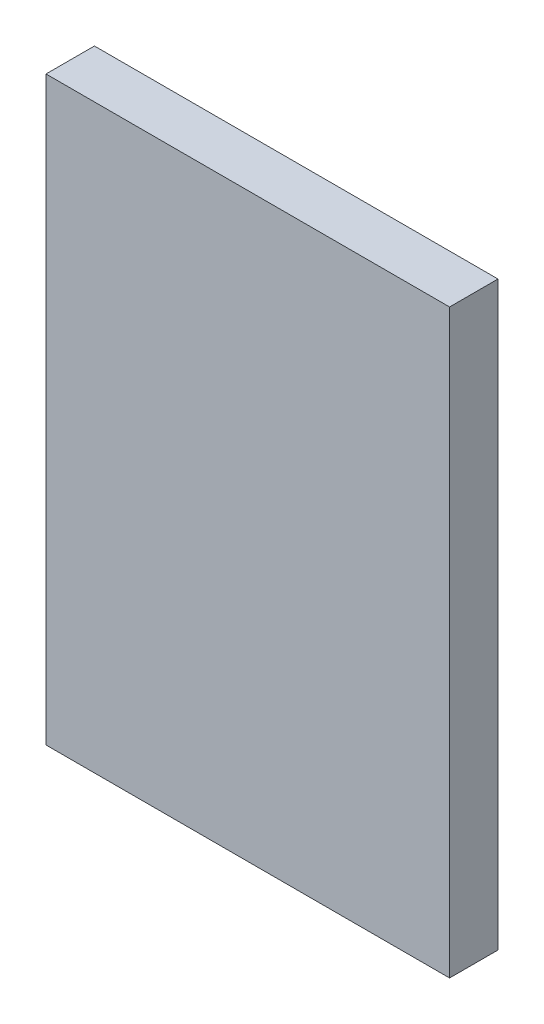
SolidWorks part; units mm, degrees
ref_plane "前视基准面" through (0, 0, 0) normal (0, 0, 1) x (1, 0, 0)
ref_plane "上视基准面" through (0, 0, 0) normal (0, 1, 0) x (1, 0, 0)
ref_plane "右视基准面" through (0, 0, 0) normal (1, 0, 0) x (0, 0, -1)
sketch "草图1" plane through (0, 0, 0) normal (0, 0, 1) x (1, 0, 0)
  line L1 (-6.3516, 7.5203) -> (18.6484, 7.5203)
  line L2 (-6.3516, 7.5203) -> (-6.3516, -28.4797)
  line L3 (-6.3516, -28.4797) -> (18.6484, -28.4797)
  line L4 (18.6484, 7.5203) -> (18.6484, -28.4797)
  dimension "D1" = 25
  dimension "D2" = 36
extrude "凸台-拉伸1" add sketch "草图1" along normal blind 3
